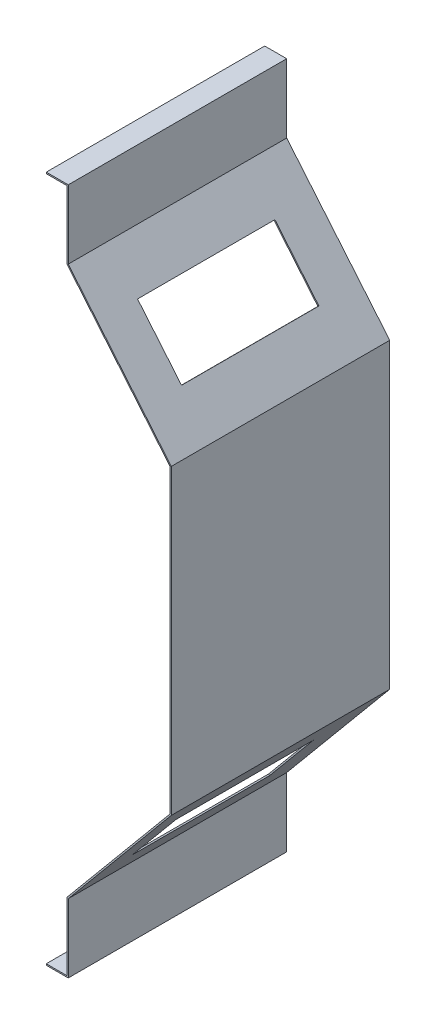
SolidWorks part; units mm, degrees
material "1023 Carbon Steel Sheet (SS)"
ref_plane "Front Plane" through (0, 0, 0) normal (0, 0, 1) x (1, 0, 0)
ref_plane "Top Plane" through (0, 0, 0) normal (0, 1, 0) x (1, 0, 0)
ref_plane "Right Plane" through (0, 0, 0) normal (1, 0, 0) x (0, 0, -1)
sketch "Sketch1" plane through (0, 0, 0) normal (0, 0, 1) x (1, 0, 0)
  line L0 (0, 110) -> (0, -110)
  line L1 (-75, 249) -> (-75, 200)
  line L2 (-75, 200) -> (0, 110)
  line L3 (0, 0) -> (60.5873, 0) construction
  line L4 (0, 0) -> (-93.7086, 0) construction
  line L5 (-75, -200) -> (0, -110)
  line L6 (-75, -249) -> (-75, -200)
  line L7 (-76, 249) -> (-76, 199.638)
  line L8 (-76, 199.638) -> (-1, 109.638)
  line L9 (-1, 109.638) -> (-1, -109.638)
  line L10 (-76, -199.638) -> (-1, -109.638)
  line L11 (-76, -249) -> (-76, -199.638)
  line L14 (-76, 249) -> (-91, 249)
  line L15 (-91, 250) -> (-75, 250)
  line L16 (-75, 249) -> (-75, 250)
  line L17 (-91, 250) -> (-91, 249)
  line L18 (-91, -250) -> (-91, -249)
  line L19 (-76, -249) -> (-91, -249)
  line L20 (-91, -250) -> (-75, -250)
  line L21 (-75, -250) -> (-75, -249)
  point P4 (0, 0)
  dimension "D1" = 220
  dimension "D2" = 250
  dimension "D3" = 90
  dimension "D4" = 75
  dimension "D6" = 15
  dimension "D7" = 1
  dimension "D8" = 250
  dimension "D9" = 117.1537
  dimension "D10" = 50
  dimension "D11" = 16
  dimension "D5" = 1
extrude "Boss-Extrude1" add sketch "Sketch1" along normal blind 159
sketch "Sketch2" plane through (54.0984, -45.082, 0) normal (0.7682, -0.6402, 0) x (0, 0, -1)
  line L0 (-159, -84.5043) -> (0, -84.5043) construction
  line L1 (-134, -118.0043) -> (-34, -118.0043)
  line L2 (-134, -118.0043) -> (-134, -168.0043)
  line L3 (-134, -168.0043) -> (-34, -168.0043)
  line L4 (-34, -118.0043) -> (-34, -168.0043)
  line L5 (-134, -118.0043) -> (-34, -168.0043) construction
  line L6 (-134, -168.0043) -> (-34, -118.0043) construction
  line L8 (-159, -201.6581) -> (-159, -84.5043) construction
  line L9 (-159, -201.6581) -> (0, -201.6581) construction
  point P0 (-84, -143.0043)
  dimension "D1" = 58.5
  dimension "D2" = 75
  dimension "D3" = 50
  dimension "D4" = 100
  dimension "D5" = 58.6537
extrude "Cut-Extrude1" cut sketch "Sketch2" against normal blind 160
sketch "Sketch5" plane through (54.0984, 45.082, 0) normal (0.7682, 0.6402, 0) x (0, 0, -1)
  line L1 (-130, 168.1581) -> (-30, 168.1581)
  line L2 (-130, 168.1581) -> (-130, 118.1581)
  line L3 (-130, 118.1581) -> (-30, 118.1581)
  line L4 (-30, 168.1581) -> (-30, 118.1581)
  line L5 (-130, 168.1581) -> (-30, 118.1581) construction
  line L6 (-130, 118.1581) -> (-30, 168.1581) construction
  line L7 (0, 84.5043) -> (0, 201.6581) construction
  line L8 (-159, 201.6581) -> (0, 201.6581) construction
  point P0 (-80, 143.1581)
  dimension "D1" = 80
  dimension "D2" = 50
  dimension "D3" = 100
  dimension "D4" = 58.5
extrude "Cut-Extrude2" cut sketch "Sketch5" against normal blind 160
